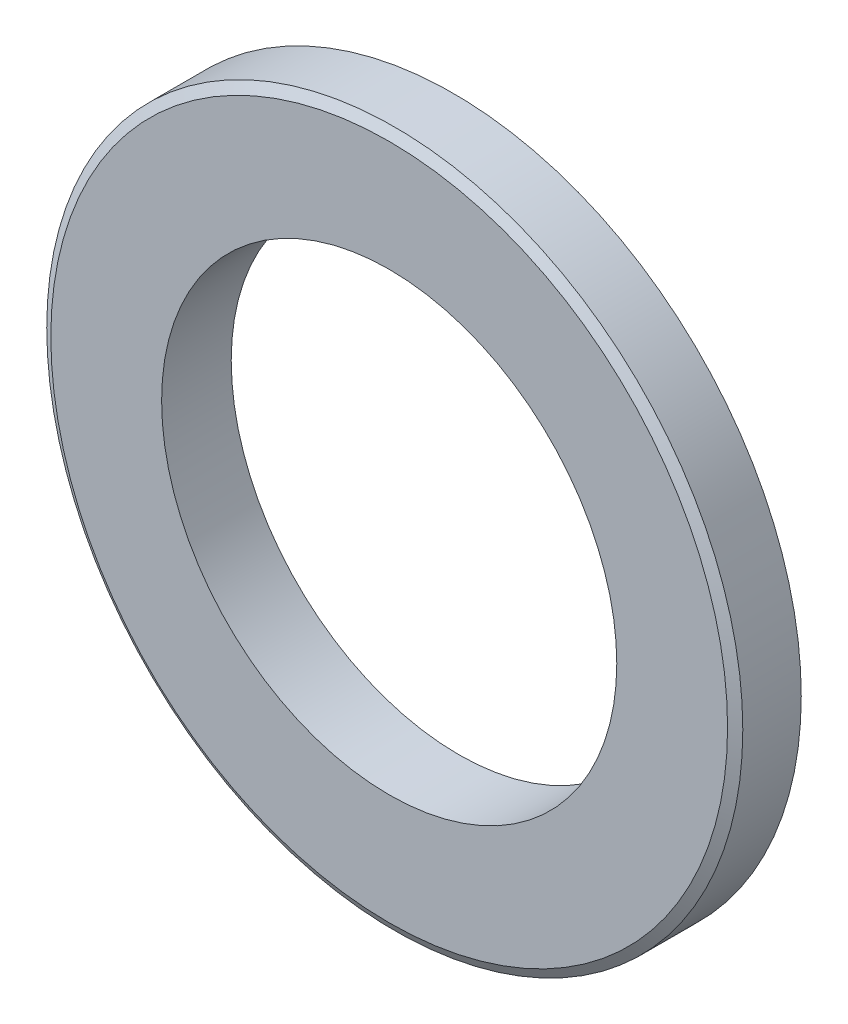
SolidWorks part; units mm, degrees
other "Imported1" parameters "D1"=0.254
material "Leaded Commercial Bronze"
ref_plane "Front Plane" through (0, 0, 0) normal (0, 0, 1) x (1, 0, 0)
ref_plane "Top Plane" through (0, 0, 0) normal (0, 1, 0) x (1, 0, 0)
ref_plane "Right Plane" through (0, 0, 0) normal (1, 0, 0) x (0, 0, -1)
sketch "Sketch1" plane through (0, 0, 0) normal (0, 0, 1) x (1, 0, 0)
  line L0 (-15.875, 0) -> (15.875, 0) construction
  line L1 (-9.5504, 0) -> (9.5504, 0) construction
  circle A0 centre (0, 0) radius 9.5504 construction
  circle A1 centre (0, 0) radius 15.875 construction
  point P8 (0, 0)
  point P9 (0, 15.875)
  point P11 (9.5504, 0)
  dimension "ID" = 19.1008
  dimension "OD" = 31.75
sketch "Sketch2" plane through (0, 0, 0) normal (1, 0, 0) x (0, 0, -1)
  line L0 (-1.5875, 15.875) -> (1.5875, 15.875) construction
  point P2 (0, 15.875)
  dimension "Thickness" = 3.175
sketch "Sketch3" plane through (0, 0, 0) normal (0, 0, 1) x (1, 0, 0)
  circle A0 centre (0, 0) radius 9.5504
  circle A1 centre (0, 0) radius 15.875
extrude "Boss-Extrude1" add sketch "Sketch3" along normal up to vertex (1.5875 mm away) and the other way up to vertex (1.5875 mm away) up to point (0, 15.875, 1.5875) other way up to point (0, 15.875, -1.5875)
chamfer "Chamfer1" distance 0.254 angle 60 2 edges at (15.875, 0, -1.5875) (15.875, 0, 1.5875)
sketch "Sketch4" plane through (0, 0, 0) normal (1, 0, 0) x (0, 0, -1)
  line L3 (-1.5875, 9.4996) -> (-1.5875, 9.6012)
  line L4 (-1.5875, 9.4996) -> (1.5875, 9.4996)
  line L5 (1.5875, 9.4996) -> (1.5875, 9.6012)
  line L6 (-1.5875, 0) -> (1.5875, 0) construction
  arc A0 (-1.5875, 9.6012) -> (1.5875, 9.6012) centre (0, 34.3805) ccw
  point P0 (0, 9.5504)
  point P9 (-1.5875, 9.5504)
  point P13 (0, 0)
  dimension "D1" = 0.0508
revolve "Cut-Revolve1" cut sketch "Sketch4" angle 360 about L6
chamfer "Chamfer2" distance 0.254 angle 60 2 edges at (0, -9.6012, -1.5875) (0, -9.6012, 1.5875)
sketch "Sketch5" plane through (0, 0, 1.5875) normal (0, 0, 1) x (1, 0, 0)
  circle A0 centre (0, 0) radius 10.381
  dimension "D1" = 20.762
extrude "Cut-Extrude1" cut sketch "Sketch5" against normal through all
equation "\"D1@Chamfer2\"=\"D1@Chamfer1\""
equation "\"D1@Sketch5\"=20mm+0.03"
